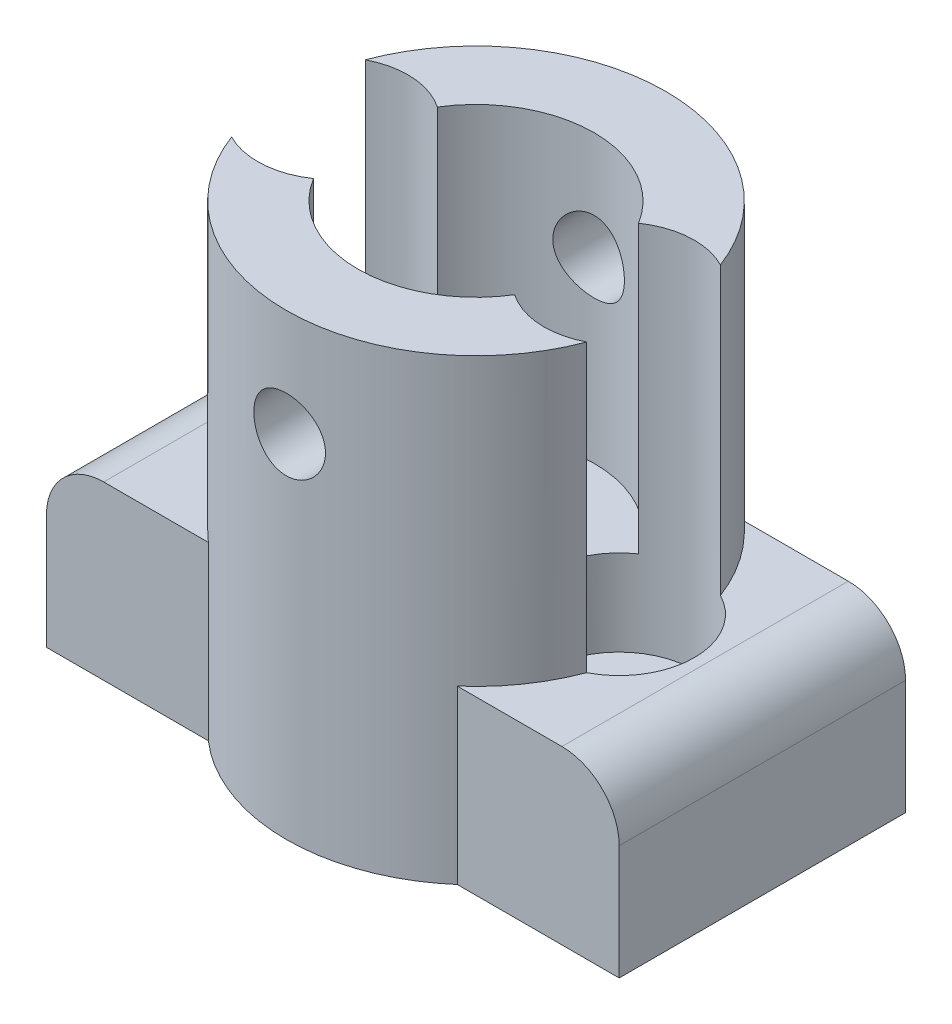
SolidWorks part; units mm, degrees
ref_plane "Front Plane" through (0, 0, 0) normal (0, 0, 1) x (1, 0, 0)
ref_plane "Top Plane" through (0, 0, 0) normal (0, 1, 0) x (1, 0, 0)
ref_plane "Right Plane" through (0, 0, 0) normal (1, 0, 0) x (0, 0, -1)
sketch "Sketch1" plane through (0, 0, 0) normal (0, 1, 0) x (1, 0, 0)
  line L1 (-20, -10) -> (20, -10)
  line L2 (-20, -10) -> (-20, 10)
  line L3 (-20, 10) -> (20, 10)
  line L4 (20, -10) -> (20, 10)
  line L5 (-20, -10) -> (20, 10) construction
  line L6 (-20, 10) -> (20, -10) construction
  point P0 (0, 0)
  dimension "D1" = 40
  dimension "D2" = 20
extrude "Boss-Extrude1" add sketch "Sketch1" along normal blind 12
hole_wizard "CBORE for M5 SHCS1" positions "Sketch3" profile "Sketch2" counterbore size "M5" standard "ANSI Metric" end condition up to next
sketch "Sketch3" plane through (0, 12, 0) normal (0, 1, 0) x (1, 0, 0)
  line L0 (0, 0) -> (0, 10) construction
  line L1 (20, 10) -> (-20, 10) construction
  point P0 (10, 0)
  point P2 (-10, 0)
  dimension "D1" = 10
  dimension "D2" = 10
sketch "Sketch2" plane through (10, 12, 0) normal (1, 0, 0) x (0, 0, 1)
  line L0 (0, 0) -> (0, 12)
  line L1 (0, 12) -> (2.75, 12)
  line L3 (2.75, 12) -> (2.75, 6)
  line L4 (2.75, 6) -> (5.25, 6)
  line L5 (5.25, 6) -> (5.25, 0)
  line L7 (5.25, 0) -> (0, 0)
  line L11 (0, -6.35) -> (0, 107.95) construction
  dimension "Thru Hole Dia." = 5.5
  dimension "Thru Hole Depth" = 12
  dimension "C'Bore Dia." = 10.5
  dimension "C'Bore Depth" = 6
sketch "Sketch4" plane through (0, 12, 0) normal (0, 1, 0) x (1, 0, 0)
  arc A0 (-12.4, -4.6693) -> (12.4, -4.6693) centre (0, 0) ccw
  arc A1 (-7.025, -4.3257) -> (7.025, -4.3257) centre (0, 0) ccw
  circle A2 centre (10, 0) radius 5.25 construction
  circle A3 centre (-10, 0) radius 5.25 construction
  arc A4 (7.025, -4.3257) -> (12.4, -4.6693) centre (10, 0) ccw
  arc A5 (-12.4, -4.6693) -> (-7.025, -4.3257) centre (-10, 0) ccw
  arc A6 (-7.025, 4.3257) -> (-12.4, 4.6693) centre (-10, 0) ccw
  arc A7 (7.025, 4.3257) -> (-7.025, 4.3257) centre (0, 0) ccw
  arc A8 (12.4, 4.6693) -> (-12.4, 4.6693) centre (0, 0) ccw
  arc A9 (12.4, 4.6693) -> (7.025, 4.3257) centre (10, 0) ccw
  dimension "D1" = 5
  dimension "D2" = 16.5
  dimension "D3" = 13.25
extrude "Boss-Extrude2" add sketch "Sketch4" along normal blind 20 and the other way up to surface (12 mm away) other way up to face at (10, 0, -2.75)
sketch "Sketch6" plane through (0, 0, 0) normal (0, 0, 1) x (1, 0, 0)
  line L0 (0, 32) -> (0, 0) construction
  line L1 (12.4, 32) -> (-12.4, 32) construction
  line L2 (12.4, 24.5) -> (-12.4, 24.5) construction
  line L3 (12.4, 32) -> (12.4, 12) construction
  line L4 (-12.4, 32) -> (-12.4, 12) construction
  line L5 (-8.6927, 12) -> (-20, 12) construction
  circle A0 centre (0, 24.5) radius 2.5
  dimension "D2" = 5
  dimension "D1" = 12.5
extrude "Cut-Extrude1" cut sketch "Sketch6" against normal through all both and the other way through all
fillet "Fillet1" radius 4 2 edges at (-20, 12, 0) (20, 12, 0)
